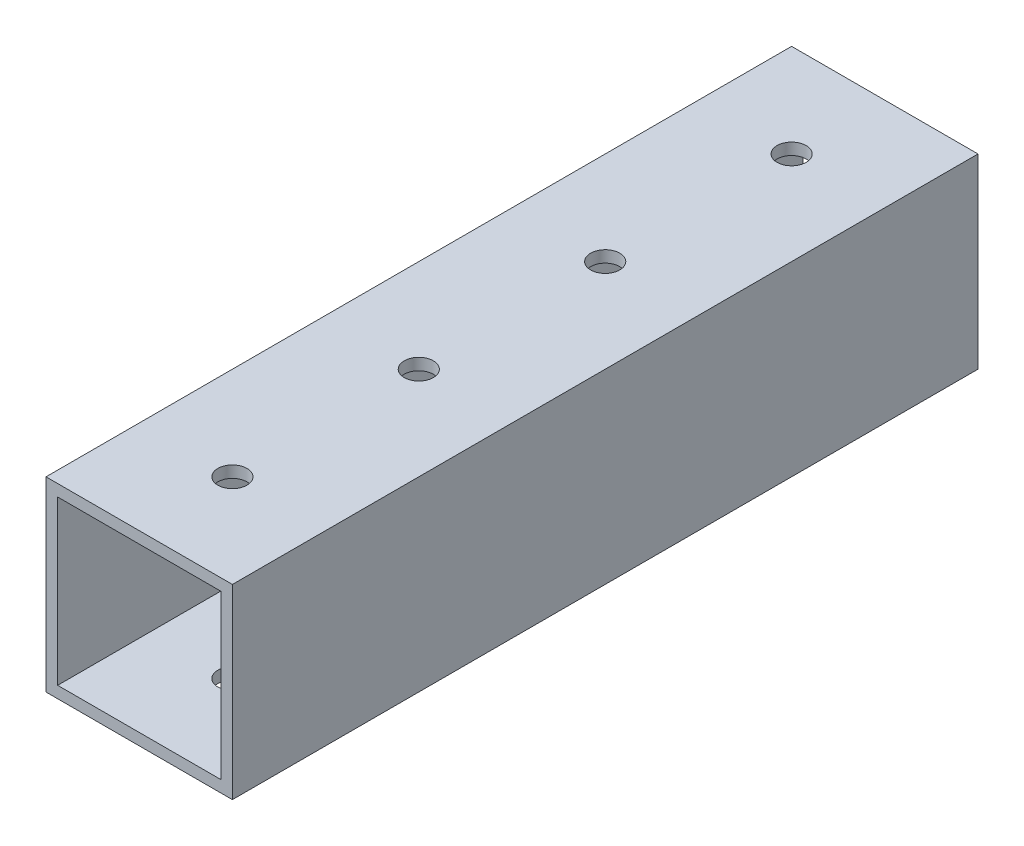
SolidWorks part; units mm, degrees
ref_plane "Front Plane" through (0, 0, 0) normal (0, 0, 1) x (1, 0, 0)
ref_plane "Top Plane" through (0, 0, 0) normal (0, 1, 0) x (1, 0, 0)
ref_plane "Right Plane" through (0, 0, 0) normal (1, 0, 0) x (0, 0, -1)
sketch "Sketch1" plane through (0, 0, 0) normal (0, 0, 1) x (1, 0, 0)
  line L1 (-11.1125, 11.1125) -> (11.1125, 11.1125)
  line L2 (-11.1125, 11.1125) -> (-11.1125, -11.1125)
  line L3 (-11.1125, -11.1125) -> (11.1125, -11.1125)
  line L4 (11.1125, 11.1125) -> (11.1125, -11.1125)
  line L5 (-11.1125, 11.1125) -> (11.1125, -11.1125) construction
  line L6 (-11.1125, -11.1125) -> (11.1125, 11.1125) construction
  line L7 (-12.7, 12.7) -> (12.7, 12.7)
  line L8 (-12.7, 12.7) -> (-12.7, -12.7)
  line L9 (-12.7, -12.7) -> (12.7, -12.7)
  line L10 (12.7, 12.7) -> (12.7, -12.7)
  line L11 (-12.7, 12.7) -> (12.7, -12.7) construction
  line L12 (-12.7, -12.7) -> (12.7, 12.7) construction
  point P0 (0, 0)
  point P6 (0, 0)
  dimension "D1" = 25.4
  dimension "D2" = 25.4
  dimension "D3" = 1.5875
extrude "Boss-Extrude1" add sketch "Sketch1" along normal blind 101.6
sketch "Sketch2" plane through (0, 12.7, 0) normal (0, 1, 0) x (1, 0, 0)
  line L0 (0, -101.6) -> (0, -88.9) construction
  line L1 (12.7, -101.6) -> (-12.7, -101.6) construction
  circle A0 centre (0, -88.9) radius 1.9844
  circle A1 centre (0, -63.5) radius 1.9844
  circle A2 centre (0, -38.1) radius 1.9844
  circle A3 centre (0, -12.7) radius 1.9844
  circle A4 centre (0, 12.7) radius 1.9844
  circle A5 centre (0, 38.1) radius 1.9844
  circle A6 centre (0, 63.5) radius 1.9844
  circle A7 centre (0, 88.9) radius 1.9844
  circle A8 centre (0, 114.3) radius 1.9844
  circle A9 centre (0, 139.7) radius 1.9844
  circle A10 centre (0, 165.1) radius 1.9844
  circle A11 centre (0, 190.5) radius 1.9844
  dimension "D2" = 3.9688
  dimension "D1" = 12.7
  dimension "D3" = 12
extrude "Cut-Extrude1" cut sketch "Sketch2" against normal through all
